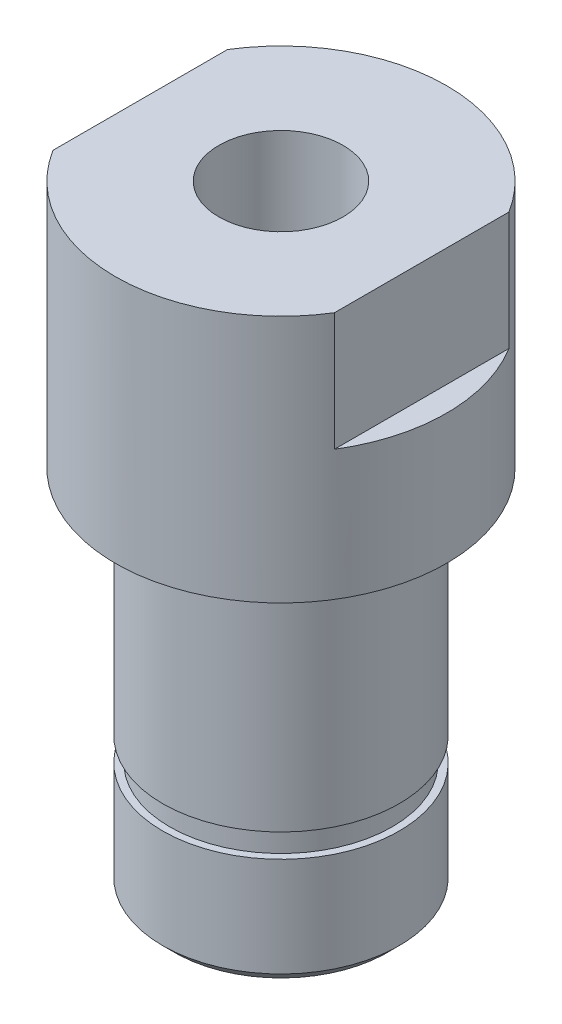
SolidWorks part; units mm, degrees
material "1.0037 (S235JR)"
ref_plane "Front Plane" through (0, 0, 0) normal (0, 0, 1) x (1, 0, 0)
ref_plane "Top Plane" through (0, 0, 0) normal (0, 1, 0) x (1, 0, 0)
ref_plane "Right Plane" through (0, 0, 0) normal (1, 0, 0) x (0, 0, -1)
sketch "Sketch1" plane through (0, 0, 0) normal (0, 1, 0) x (1, 0, 0)
  circle A0 centre (0, 0) radius 14
  dimension "D1" = 28
extrude "Boss-Extrude1" add sketch "Sketch1" along normal blind 6
sketch "Sketch2" plane through (0, 0, 0) normal (0, -1, 0) x (1, 0, 0)
  circle A0 centre (0, 0) radius 14
  dimension "D1" = 28
extrude "Boss-Extrude2" add sketch "Sketch2" along normal blind 15
sketch "Sketch3" plane through (0, -15, 0) normal (0, -1, 0) x (1, 0, 0)
  circle A0 centre (0, 0) radius 10
  dimension "D1" = 20
extrude "Boss-Extrude3" add sketch "Sketch3" along normal blind 31
hole_wizard "Ø10.5 (10.5) Diameter Hole1" positions "3DSketch2" profile "Sketch4" hole size "Ø10.5" standard "BSI"
sketch3d "3DSketch2"
  line L0 (0, 6, 0) -> (0, -15, 0) construction
  point P0 (0, 6, 0)
sketch "Sketch4" plane through (0, 6, 0) normal (1, 0, 0) x (0, 0, 1)
  line L0 (0, 0) -> (0, 25.1545)
  line L1 (0, 25.1545) -> (5.25, 22)
  line L2 (5.25, 22) -> (5.25, 0)
  line L5 (5.25, 0) -> (0, 0)
  line L10 (0, 25.1545) -> (-5.25, 22) construction
  line L11 (0, -6.35) -> (0, 107.95) construction
  dimension "Hole Dia." = 10.5
  dimension "Hole Depth" = 22
  dimension "Drill Angle" = 118
chamfer "Chamfer1" distance 1 angle 45 1 edges at (0, -46, -10)
sketch "Sketch5" plane through (0, 6, 0) normal (0, 1, 0) x (1, 0, 0)
  line L0 (-11.9, 16.7854) -> (-18.1414, 16.7854)
  line L2 (11.9, -16.7854) -> (11.9, 16.7854)
  line L4 (-11.9, -16.7854) -> (-11.9, 16.7854)
  line L7 (-18.1414, 16.7854) -> (-18.1414, -16.7854)
  line L8 (-18.1414, -16.7854) -> (-11.9, -16.7854)
  line L9 (11.9, 16.7854) -> (15.7038, 16.7854)
  line L10 (15.7038, 16.7854) -> (15.7038, -16.7854)
  line L11 (15.7038, -16.7854) -> (11.9, -16.7854)
  point P0 (0, 0)
  dimension "D1" = 11.9
  dimension "D2" = 11.9
extrude "Cut-Extrude2" cut sketch "Sketch5" against normal blind 10
sketch "Sketch6" plane through (0, 0, 0) normal (1, 0, 0) x (0, 0, -1)
  line L0 (-10, -15) -> (-10, -45) construction
  line L1 (-10.6, -34.6) -> (-9.4, -34.6)
  line L2 (-10.6, -34.6) -> (-10.6, -36.6)
  line L3 (-10.6, -36.6) -> (-9.4, -36.6)
  line L4 (-9.4, -34.6) -> (-9.4, -36.6)
  line L5 (-10.6, -34.6) -> (-9.4, -36.6) construction
  line L6 (-10.6, -36.6) -> (-9.4, -34.6) construction
  line L7 (-10, -15) -> (10, -15) construction
  point P0 (-10, -35.6)
  point P9 (-9.4, -35.6)
  dimension "D1" = 2
  dimension "D2" = 20.6
  dimension "D3" = 0.6
revolve "Cut-Revolve1" cut sketch "Sketch6" angle 360 about axis through (0, -46, 0) along (0, 1, 0)
